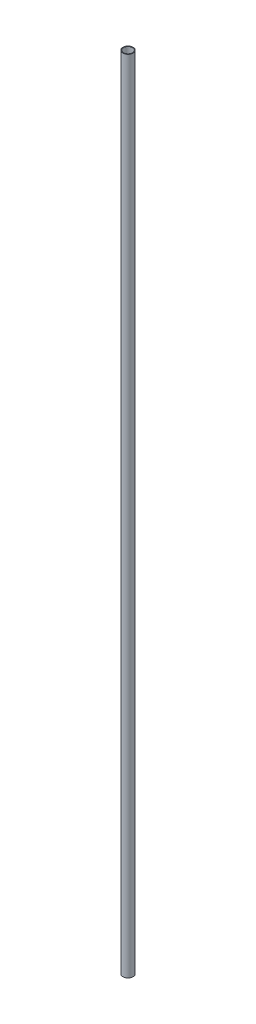
SolidWorks part; units mm, degrees
material "S-Glass Fiber"
ref_plane "Front Plane" through (0, 0, 0) normal (0, 0, 1) x (1, 0, 0)
ref_plane "Top Plane" through (0, 0, 0) normal (0, 1, 0) x (1, 0, 0)
ref_plane "Right Plane" through (0, 0, 0) normal (1, 0, 0) x (0, 0, -1)
sketch "Sketch1" plane through (0, 0, 0) normal (0, 1, 0) x (1, 0, 0)
  circle A0 centre (0, 0) radius 20
  circle A1 centre (0, 0) radius 17.46
  dimension "D1" = 40
  dimension "D2" = 2.54
extrude "Boss-Extrude1" add sketch "Sketch1" along normal blind 3131.82
sketch3d "3DSketch1" plane through (0, 0, 0) normal (0, 0, 1) x (1, 0, 0)
  dimension "D1" = 355.6
